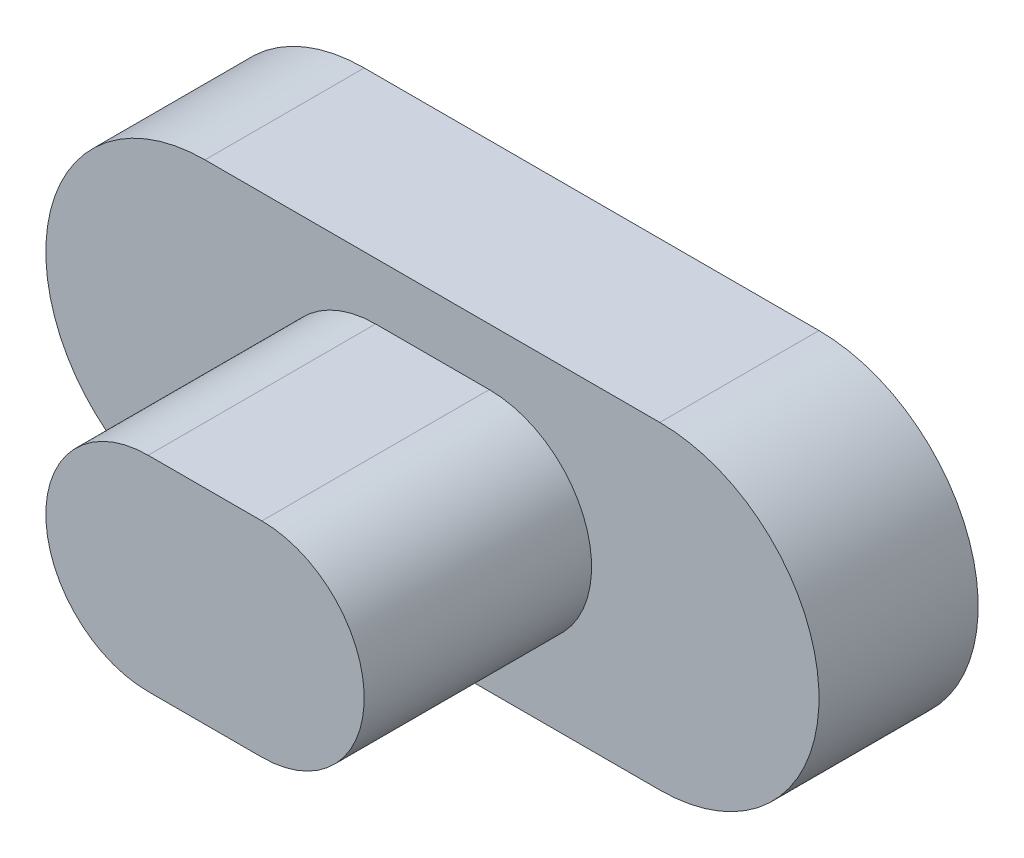
SolidWorks part; units mm, degrees
ref_plane "前视基准面" through (0, 0, 0) normal (0, 0, 1) x (1, 0, 0)
ref_plane "上视基准面" through (0, 0, 0) normal (0, 1, 0) x (1, 0, 0)
ref_plane "右视基准面" through (0, 0, 0) normal (1, 0, 0) x (0, 0, -1)
other "Configuration Table"
sketch "草图2" plane through (0, 0, 0) normal (0, 0, 1) x (1, 0, 0)
  line L0 (-2, 0) -> (2, 0) construction
  line L1 (-2, 1.4) -> (2, 1.4)
  line L2 (-2, -1.4) -> (2, -1.4)
  arc A0 (-2, 1.4) -> (-2, -1.4) centre (-2, 0) ccw
  arc A1 (2, -1.4) -> (2, 1.4) centre (2, 0) ccw
  point P2 (0, 0)
  dimension "D1" = 1.4
  dimension "D2" = 4
extrude "凸台-拉伸1" add sketch "草图2" along normal blind 1.4
sketch "草图3" plane through (0, 0, 1.4) normal (0, 0, 1) x (1, 0, 0)
  line L0 (-0.5, 0) -> (0.5, 0) construction
  line L1 (-0.5, 0.9) -> (0.5, 0.9)
  line L2 (-0.5, -0.9) -> (0.5, -0.9)
  arc A0 (-0.5, 0.9) -> (-0.5, -0.9) centre (-0.5, 0) ccw
  arc A1 (0.5, -0.9) -> (0.5, 0.9) centre (0.5, 0) ccw
  point P2 (0, 0)
  dimension "D1" = 0.9
  dimension "D2" = 1
extrude "凸台-拉伸2" add sketch "草图3" along normal blind 2
sketch "草图4" plane through (0, 0, 0) normal (0, 0, -1) x (-1, 0, 0)
  line L1 (-0.8, 0.6) -> (0.8, 0.6)
  line L2 (-0.8, 0.6) -> (-0.8, -0.6)
  line L3 (-0.8, -0.6) -> (0.8, -0.6)
  line L4 (0.8, 0.6) -> (0.8, -0.6)
  line L5 (-0.8, 0.6) -> (0.8, -0.6) construction
  line L6 (-0.8, -0.6) -> (0.8, 0.6) construction
  point P0 (0, 0)
  dimension "D1" = 1.2
  dimension "D2" = 1.6
extrude "切除-拉伸1" cut sketch "草图4" against normal blind 2
